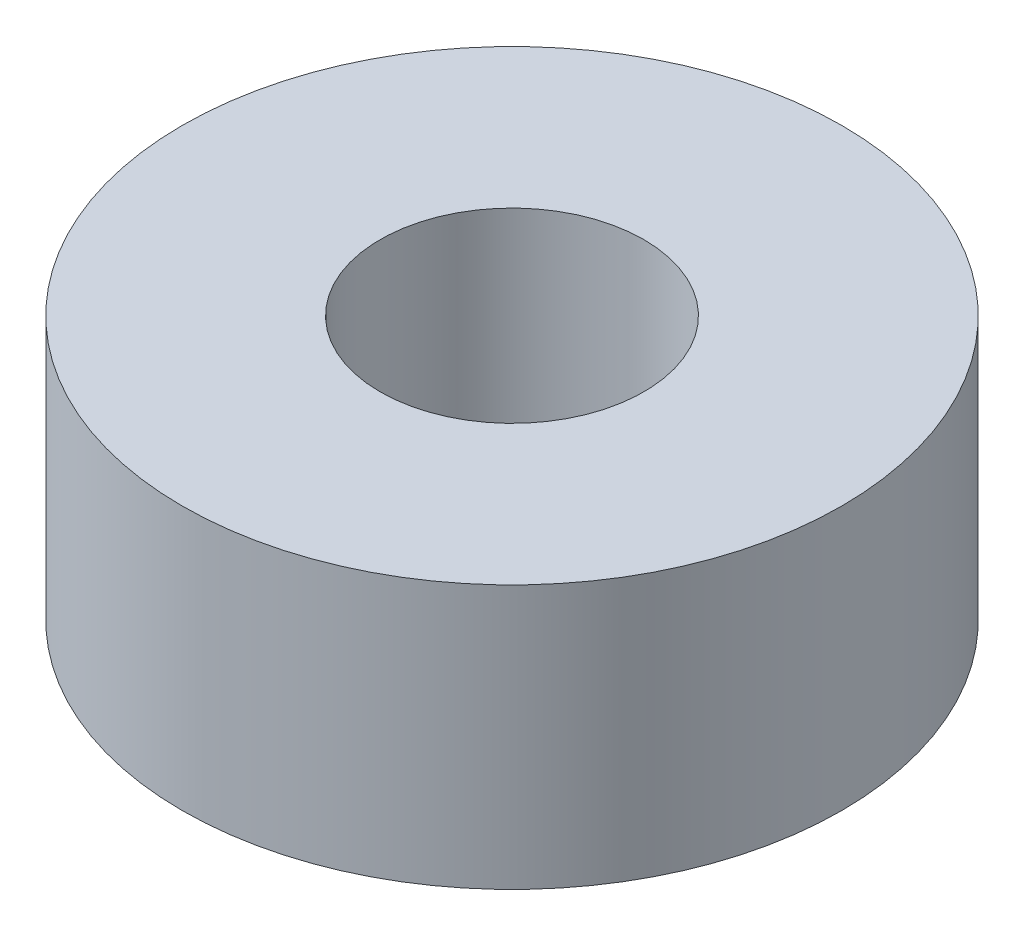
SolidWorks part; units mm, degrees
material "Plain Carbon Steel"
ref_plane "Front Plane" through (0, 0, 0) normal (0, 0, 1) x (1, 0, 0)
ref_plane "Top Plane" through (0, 0, 0) normal (0, 1, 0) x (1, 0, 0)
ref_plane "Right Plane" through (0, 0, 0) normal (1, 0, 0) x (0, 0, -1)
sketch "Sketch1" plane through (0, 0, 0) normal (0, 1, 0) x (1, 0, 0)
  circle A0 centre (0, 0) radius 5
  circle A1 centre (0, 0) radius 12.5
  dimension "D1" = 10
  dimension "D2" = 25
extrude "Boss-Extrude1" add sketch "Sketch1" along normal blind 10
